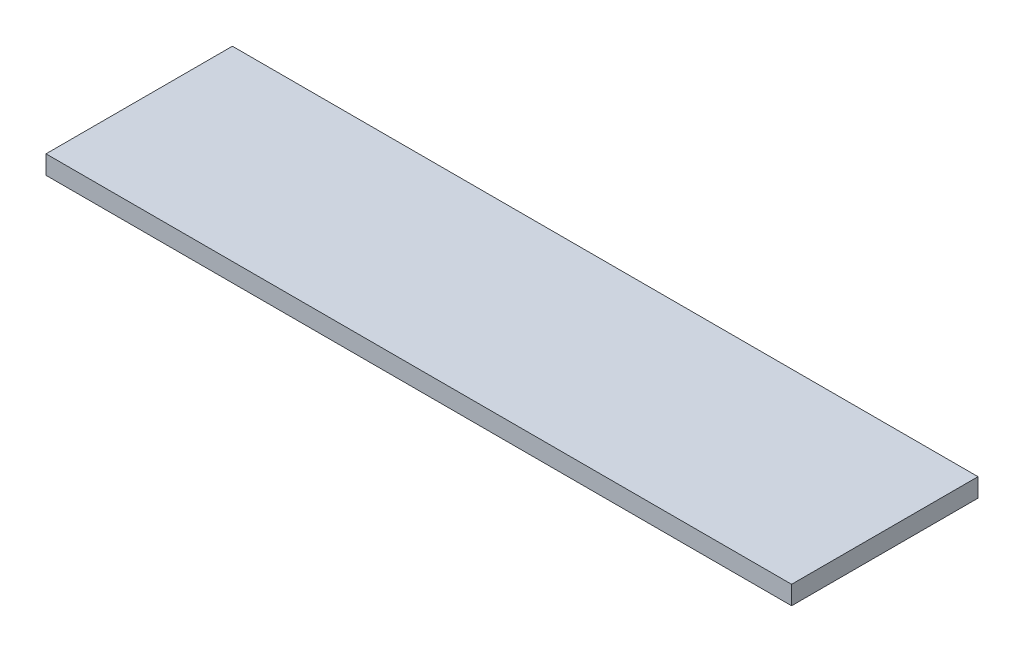
SolidWorks part; units mm, degrees
ref_plane "Спереди" through (0, 0, 0) normal (0, 0, 1) x (1, 0, 0)
ref_plane "Сверху" through (0, 0, 0) normal (0, 1, 0) x (1, 0, 0)
ref_plane "Справа" through (0, 0, 0) normal (1, 0, 0) x (0, 0, -1)
sketch "Эскиз2" plane through (0, 0, 0) normal (0, 1, 0) x (1, 0, 0)
  line L1 (-400, 100) -> (400, 100)
  line L3 (-400, -100) -> (400, -100)
  line L4 (400, 100) -> (400, -100)
  line L5 (-400, 100) -> (400, -100) construction
  line L6 (-400, -100) -> (400, 100) construction
  line L7 (-400, -100) -> (-400, 100)
  line L8 (-222.2289, 0) -> (202.2563, 0) construction
  point P0 (0, 0)
  dimension "D1" = 800
extrude "Бобышка-Вытянуть1" add sketch "Эскиз2" along normal blind 20
